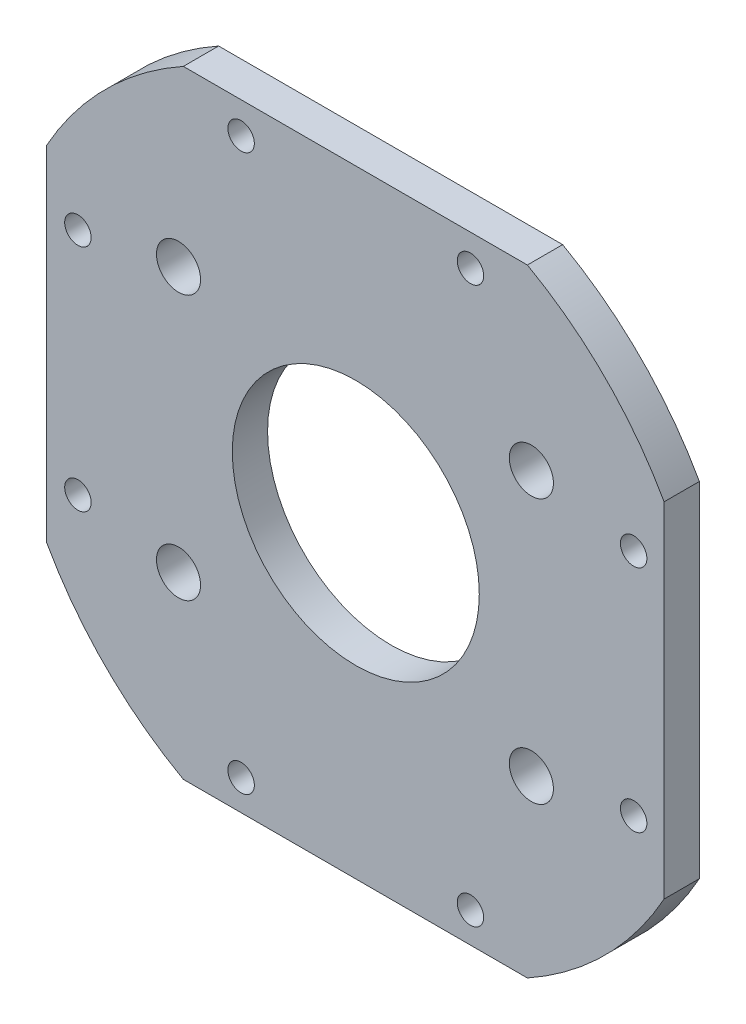
SolidWorks part; units mm, degrees
ref_plane "Front Plane" through (0, 0, 0) normal (0, 0, 1) x (1, 0, 0)
ref_plane "Top Plane" through (0, 0, 0) normal (0, 1, 0) x (1, 0, 0)
ref_plane "Right Plane" through (0, 0, 0) normal (1, 0, 0) x (0, 0, -1)
sketch "Sketch1" plane through (0, 0, 0) normal (0, 0, 1) x (1, 0, 0)
  line L0 (-19.5, 35) -> (19.5, 35)
  line L1 (19.5, 35) -> (35, 19.5) construction
  line L2 (35, 19.5) -> (35, -19.5)
  line L3 (35, -19.5) -> (19.5, -35) construction
  line L4 (19.5, -35) -> (-19.5, -35)
  line L5 (-19.5, -35) -> (-35, -19.5) construction
  line L6 (-35, -19.5) -> (-35, 19.5)
  line L7 (-35, 19.5) -> (-19.5, 35) construction
  line L8 (-19.5, 35) -> (19.5, -35) construction
  line L9 (-20.0482, 15.0482) -> (19.9518, -14.9518) construction
  line L10 (-20.0482, 15.0482) -> (19.9518, 15.0482) construction
  line L11 (-20.0482, 15.0482) -> (-20.0482, -14.9518) construction
  line L12 (-20.0482, -14.9518) -> (19.9518, -14.9518) construction
  line L13 (19.9518, 15.0482) -> (19.9518, -14.9518) construction
  line L15 (-31.4518, 12.9518) -> (31.5482, 12.9518) construction
  line L16 (-31.4518, 12.9518) -> (-31.4518, -13.0482) construction
  line L17 (-31.4518, -13.0482) -> (31.5482, -13.0482) construction
  line L18 (31.5482, 12.9518) -> (31.5482, -13.0482) construction
  line L19 (-31.4518, 12.9518) -> (31.5482, -13.0482) construction
  line L20 (-31.4518, -13.0482) -> (31.5482, 12.9518) construction
  line L21 (-12.9518, 31.4518) -> (13.0482, 31.4518) construction
  line L22 (-12.9518, 31.4518) -> (-12.9518, -31.5482) construction
  line L23 (-12.9518, -31.5482) -> (13.0482, -31.5482) construction
  line L24 (13.0482, 31.4518) -> (13.0482, -31.5482) construction
  line L25 (-12.9518, 31.4518) -> (13.0482, -31.5482) construction
  line L26 (-12.9518, -31.5482) -> (13.0482, 31.4518) construction
  arc A0 (-19.5, 35) -> (-35, 19.5) centre (-0.0482, 0.0482) ccw
  arc A1 (19.5, 35) -> (35, 19.5) centre (0.0482, 0.0482) cw
  arc A2 (35, -19.5) -> (19.5, -35) centre (0.0482, -0.0482) cw
  arc A3 (-35, -19.5) -> (-19.5, -35) centre (-0.0482, -0.0482) ccw
  circle A4 centre (-20.0482, 15.0482) radius 2.5
  circle A5 centre (19.9518, 15.0482) radius 2.5
  circle A6 centre (-20.0482, -14.9518) radius 2.5
  circle A7 centre (19.9518, -14.9518) radius 2.5
  circle A8 centre (-12.9518, 31.4518) radius 1.5
  circle A9 centre (13.0482, 31.4518) radius 1.5
  circle A10 centre (31.5482, 12.9518) radius 1.5
  circle A11 centre (31.5482, -13.0482) radius 1.5
  circle A12 centre (13.0482, -31.5482) radius 1.5
  circle A13 centre (-12.9518, -31.5482) radius 1.5
  circle A14 centre (-31.4518, -13.0482) radius 1.5
  circle A15 centre (-31.4518, 12.9518) radius 1.5
  circle A16 centre (0.0482, -0.0482) radius 14
  point P12 (0, 0)
  point P22 (-0.0482, 0.0482)
  dimension "D2" = 40
  dimension "D5" = 5
  dimension "D10" = 3
  dimension "D11" = 28
  dimension "D1" = 70
  dimension "D3" = 39
  dimension "D4" = 70
  dimension "D6" = 30
  dimension "D7" = 40
  dimension "D8" = 26
  dimension "D9" = 63
extrude "Boss-Extrude1" add sketch "Sketch1" along normal blind 4
